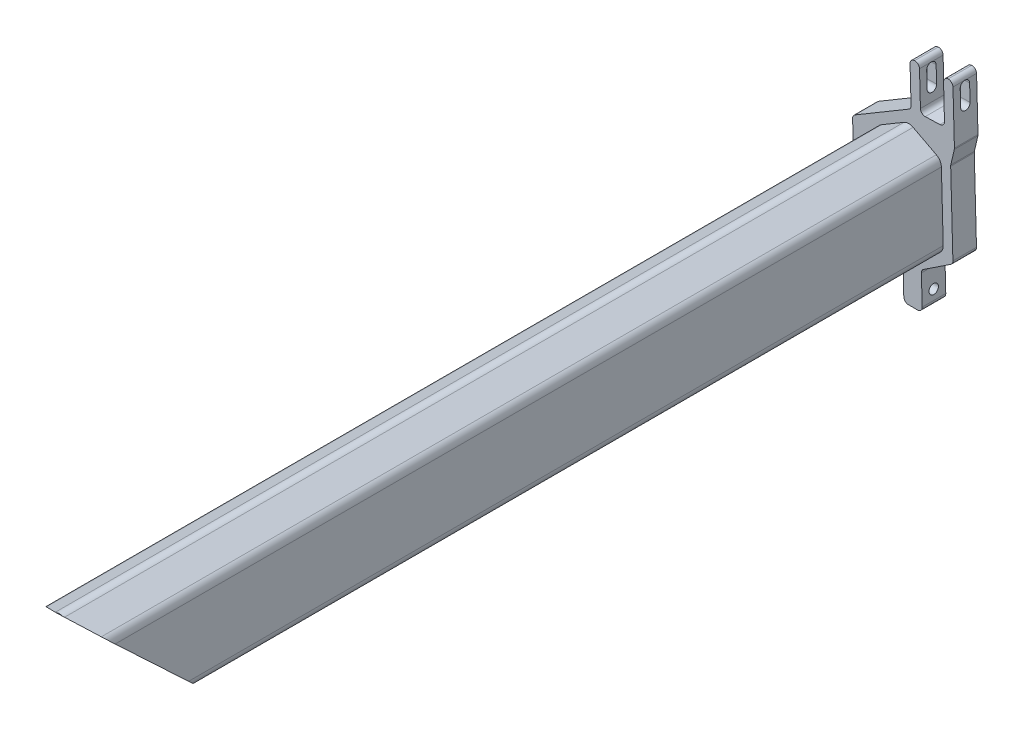
SolidWorks part; units mm, degrees
other "Markup1"
sketch "Sketch4" plane through (238.7089, 157.952, 185) normal (0.151, -0.0403, 0.9877) x (-0.3193, -0.9476, 0.0101)
ref_plane "Front Plane" through (0, 0, 0) normal (0, 0, 1) x (1, 0, 0)
ref_plane "Top Plane" through (0, 0, 0) normal (0, 1, 0) x (1, 0, 0)
ref_plane "Right Plane" through (0, 0, 0) normal (1, 0, 0) x (0, 0, -1)
sketch "Sketch1" plane through (0, 0, 0) normal (0, 0, 1) x (1, 0, 0)
  line L0 (36.798, 101.1427) -> (103.7813, 99.6461) construction
  line L1 (229.8883, 157.752) -> (228.5651, 206.1267) construction
  line L30 (217.1308, 186.237) -> (217.5229, 171.9028)
  line L32 (228.5166, 190.1025) -> (223.7423, 187.2691)
  line L33 (223.253, 186.3818) -> (223.6425, 172.1409)
  line L34 (224.1866, 171.2781) -> (229.1073, 168.7597)
  line L35 (234.8421, 171.5695) -> (230.0664, 168.7859)
  line L36 (234.9486, 186.7017) -> (235.3382, 172.4608)
  line L37 (229.4895, 190.1291) -> (234.4116, 187.5609)
  line L38 (237.9182, 187.8539) -> (238.387, 170.7148)
  line L39 (229.0267, 193.8938) -> (217.6201, 187.1243)
  line L40 (218.0669, 171.04) -> (227.2536, 166.3383)
  line L41 (229.3079, 202.3906) -> (229.516, 194.7811)
  line L42 (230.2801, 203.4176) -> (230.2809, 203.4176)
  line L43 (231.3079, 202.4453) -> (231.5047, 195.248)
  line L44 (232.5317, 194.2757) -> (235.6305, 194.3605)
  line L45 (236.6028, 195.3875) -> (236.4059, 202.5848)
  line L46 (237.3782, 203.6118) -> (237.379, 203.6118)
  line L47 (238.4059, 202.6395) -> (238.7085, 191.5789)
  line L48 (238.6835, 191.3277) -> (237.9432, 188.1051)
  line L49 (229.2805, 203.3903) -> (238.772, 203.6499) construction
  line L50 (227.7976, 165.4754) -> (227.9768, 158.9247)
  line L51 (228.9765, 157.952) -> (230.8782, 157.952)
  line L52 (231.8778, 158.9794) -> (231.7085, 165.1677)
  line L53 (232.1565, 166.0291) -> (237.939, 169.8533)
  arc A0 (223.253, 186.3818) -> (223.7423, 187.2691) centre (224.2526, 186.4091) cw
  arc A15 (234.4116, 187.5609) -> (234.9486, 186.7017) centre (233.949, 186.6744) cw
  arc A16 (235.3382, 172.4608) -> (234.8421, 171.5695) centre (234.3385, 172.4335) cw
  arc A17 (224.1866, 171.2781) -> (223.6425, 172.1409) centre (224.6422, 172.1682) cw
  arc A18 (229.1073, 168.7597) -> (230.0664, 168.7859) centre (229.5629, 169.6499) ccw
  arc A19 (228.5166, 190.1025) -> (229.4895, 190.1291) centre (229.0269, 189.2425) cw
  arc A20 (229.0267, 193.8938) -> (229.516, 194.7811) centre (228.5164, 194.7538) ccw
  arc A21 (229.3079, 202.3906) -> (230.2801, 203.4176) centre (230.3075, 202.418) cw
  arc A22 (230.2809, 203.4176) -> (231.3079, 202.4453) centre (230.3082, 202.418) cw
  arc A23 (231.5047, 195.248) -> (232.5317, 194.2757) centre (232.5044, 195.2754) ccw
  arc A24 (235.6305, 194.3605) -> (236.6028, 195.3875) centre (235.6032, 195.3601) ccw
  arc A25 (236.4059, 202.5848) -> (237.3782, 203.6118) centre (237.4056, 202.6121) cw
  arc A26 (237.379, 203.6118) -> (238.4059, 202.6395) centre (237.4063, 202.6121) cw
  arc A27 (238.7085, 191.5789) -> (238.6835, 191.3277) centre (237.7089, 191.5515) cw
  arc A28 (237.9432, 188.1051) -> (237.9182, 187.8539) centre (238.9179, 187.8812) ccw
  arc A29 (238.387, 170.7148) -> (237.939, 169.8533) centre (237.3874, 170.6874) cw
  arc A30 (232.1565, 166.0291) -> (231.7085, 165.1677) centre (232.7082, 165.195) ccw
  arc A31 (231.8778, 158.9794) -> (230.8782, 157.952) centre (230.8782, 158.952) cw
  arc A32 (228.9765, 157.952) -> (227.9768, 158.9247) centre (228.9765, 158.952) cw
  arc A33 (227.7976, 165.4754) -> (227.2536, 166.3383) centre (226.798, 165.4481) ccw
  arc A34 (218.0669, 171.04) -> (217.5229, 171.9028) centre (218.5225, 171.9302) cw
  arc A35 (217.1308, 186.237) -> (217.6201, 187.1243) centre (218.1304, 186.2643) cw
  point P24 (223.2369, 186.9692)
  point P27 (234.9326, 187.2891)
  point P30 (235.3544, 171.8681)
  point P33 (223.6588, 171.5482)
  point P36 (229.594, 168.5105)
  point P39 (228.9956, 190.3868)
  dimension "D3" = 0.2
  dimension "D2" = 1
  dimension "D1" = 67
extrude "Boss-Extrude1" add sketch "Sketch1" along normal blind 5 contours L47 | L51 A31 L52 A30 L53 A29 L38 A28 L48 A27 L47 A26 L46 A25 L45 A24 L44 A23 L43 A22 L42 A21 L41 A20 L39 A35 L30 A34 L40 A33 L50 A32
sketch "Sketch2" plane through (0, 0, 5) normal (0, 0, 1) x (1, 0, 0)
  line L0 (228.0062, 190.9625) -> (223.2319, 188.129)
  line L1 (222.2534, 186.3544) -> (222.6429, 172.1136)
  line L2 (223.731, 170.3879) -> (228.6517, 167.8695)
  line L3 (230.57, 167.922) -> (235.3457, 170.7056)
  line L4 (236.3378, 172.4882) -> (235.9482, 186.729)
  line L5 (234.8742, 188.4475) -> (229.9521, 191.0157)
  line L6 (223.253, 186.3818) -> (223.6425, 172.1409)
  line L7 (228.5166, 190.1025) -> (223.7423, 187.2691)
  line L8 (234.4116, 187.5609) -> (229.4895, 190.1291)
  line L9 (235.3382, 172.4608) -> (234.9486, 186.7017)
  line L10 (230.0664, 168.7859) -> (234.8421, 171.5695)
  line L11 (224.1866, 171.2781) -> (229.1073, 168.7597)
  line L12 (223.253, 186.3818) -> (223.6425, 172.1409)
  line L13 (228.5166, 190.1025) -> (223.7423, 187.2691)
  line L14 (234.4116, 187.5609) -> (229.4895, 190.1291)
  line L15 (235.3382, 172.4608) -> (234.9486, 186.7017)
  line L16 (230.0664, 168.7859) -> (234.8421, 171.5695)
  line L17 (224.1866, 171.2781) -> (229.1073, 168.7597)
  arc A0 (223.2319, 188.129) -> (222.2534, 186.3544) centre (224.2526, 186.4091) ccw
  arc A1 (222.6429, 172.1136) -> (223.731, 170.3879) centre (224.6422, 172.1682) ccw
  arc A2 (228.6517, 167.8695) -> (230.57, 167.922) centre (229.5629, 169.6499) ccw
  arc A3 (235.3457, 170.7056) -> (236.3378, 172.4882) centre (234.3385, 172.4335) ccw
  arc A4 (235.9482, 186.729) -> (234.8742, 188.4475) centre (233.949, 186.6744) ccw
  arc A5 (229.9521, 191.0157) -> (228.0062, 190.9625) centre (229.0269, 189.2425) ccw
  arc A6 (223.7423, 187.2691) -> (223.253, 186.3818) centre (224.2526, 186.4091) ccw
  arc A7 (229.4895, 190.1291) -> (228.5166, 190.1025) centre (229.0269, 189.2425) ccw
  arc A8 (234.9486, 186.7017) -> (234.4116, 187.5609) centre (233.949, 186.6744) ccw
  arc A9 (234.8421, 171.5695) -> (235.3382, 172.4608) centre (234.3385, 172.4335) ccw
  arc A10 (229.1073, 168.7597) -> (230.0664, 168.7859) centre (229.5629, 169.6499) ccw
  arc A11 (223.6425, 172.1409) -> (224.1866, 171.2781) centre (224.6422, 172.1682) ccw
  arc A12 (223.7423, 187.2691) -> (223.253, 186.3818) centre (224.2526, 186.4091) ccw
  arc A13 (229.4895, 190.1291) -> (228.5166, 190.1025) centre (229.0269, 189.2425) ccw
  arc A14 (234.9486, 186.7017) -> (234.4116, 187.5609) centre (233.949, 186.6744) ccw
  arc A15 (234.8421, 171.5695) -> (235.3382, 172.4608) centre (234.3385, 172.4335) ccw
  arc A16 (229.1073, 168.7597) -> (230.0664, 168.7859) centre (229.5629, 169.6499) ccw
  arc A17 (223.6425, 172.1409) -> (224.1866, 171.2781) centre (224.6422, 172.1682) ccw
  dimension "D1" = 0
  dimension "D2" = 1
extrude "Boss-Extrude2" add sketch "Sketch2" along normal blind 180
sketch "Sketch3" plane through (227.1809, 6.2143, 0) normal (-0.9996, -0.0273, 0) x (0, 0, 1)
  line L0 (185, 184.7829) -> (185, 161.3093)
  line L1 (185, 184.6565) -> (185, 184.9093) construction
  line L3 (185, 161.3093) -> (160, 161.3093)
  line L4 (160, 161.3093) -> (185, 184.7829)
  line L5 (5, 180.2075) -> (5, 165.9613) construction
  line L6 (2.5, 197.0448) -> (2.5, 151.6319) construction
  line L7 (5, 197.0448) -> (0, 197.0448) construction
  line L8 (5, 151.6319) -> (0, 151.6319) construction
  line L9 (2.5, 195.0448) -> (2.5, 191.5448) construction
  line L10 (3.5, 195.0448) -> (3.5, 191.5448)
  line L11 (1.5, 195.0448) -> (1.5, 191.5448)
  line L12 (5, 161.3093) -> (185, 161.3093) construction
  arc A0 (3.5, 195.0448) -> (1.5, 195.0448) centre (2.5, 195.0448) ccw
  arc A1 (1.5, 191.5448) -> (3.5, 191.5448) centre (2.5, 191.5448) ccw
  circle A2 centre (2.5, 154.6319) radius 1
  point P17 (2.5, 193.2948)
  dimension "D2" = 2
  dimension "D5" = 3
  dimension "D1" = 155
  dimension "D3" = 2
  dimension "D4" = 2
  dimension "D6" = 3.5
extrude "Cut-Extrude1" cut sketch "Sketch3" against normal blind 180 contours A2 | L10 A1 L11 A0 | L4 L0 L3
ref_plane "Plane5" through (234.0283, 6.4016, 0) normal (-0.9996, -0.0273, 0) x (0, 0, 1)
ref_plane "Plane6" through (-4.7328, 173.0197, 0) normal (0.0273, -0.9996, 0) x (-0.9996, -0.0273, 0)
